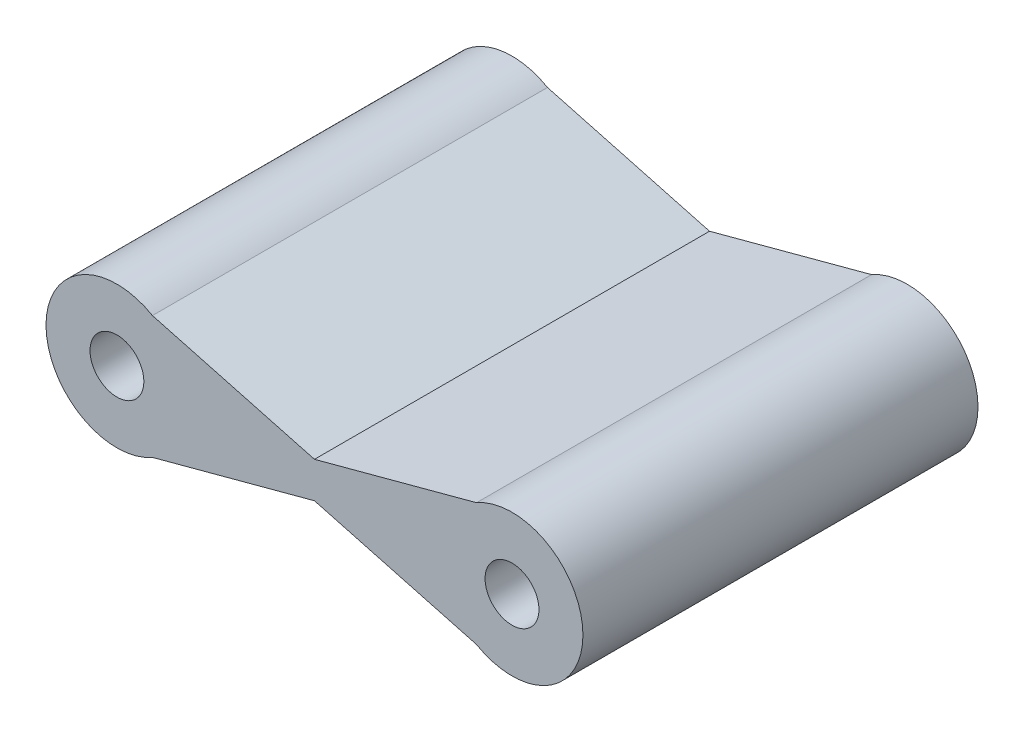
SolidWorks part; units mm, degrees
ref_plane "Front Plane" through (0, 0, 0) normal (0, 0, 1) x (1, 0, 0)
ref_plane "Top Plane" through (0, 0, 0) normal (0, 1, 0) x (1, 0, 0)
ref_plane "Right Plane" through (0, 0, 0) normal (1, 0, 0) x (0, 0, -1)
sketch "Sketch1" plane through (0, 0, 0) normal (0, 0, 1) x (1, 0, 0)
  line L0 (0, 2.475) -> (5.5, 1)
  line L1 (0, 1) -> (11, 1)
  line L2 (0, 1) -> (0, 0)
  line L3 (0, 0) -> (11, 0)
  line L4 (11, 1) -> (11, 0)
  line L5 (5.5, 1) -> (11, 2.475)
  line L6 (11, -1.475) -> (5.5, 0)
  line L7 (0, -1.475) -> (5.5, 0)
  circle A0 centre (0, 0.5) radius 1.975
  circle A1 centre (11, 0.5) radius 1.975
  circle A2 centre (0, 0.5) radius 0.75
  circle A3 centre (11, 0.5) radius 0.75
  dimension "D3" = 3.95
  dimension "D4" = 1.5
  dimension "D1" = 1
  dimension "D2" = 11
extrude "Boss-Extrude1" add sketch "Sketch1" along normal blind 11 contours L1 A0 L0 L7 L3 L2 | L3 A0 L1 L2 | A1 L1 A0 L3 | A0 L1 L0 | A1 L5 L1 | L5 A1 L1 L4 L3 L6 | L1 A1 L3 L4 | A1 L3 L6 | A0 L7 L3 | L5 A1 | L6 A1 | L7 A0 | L0 A0
